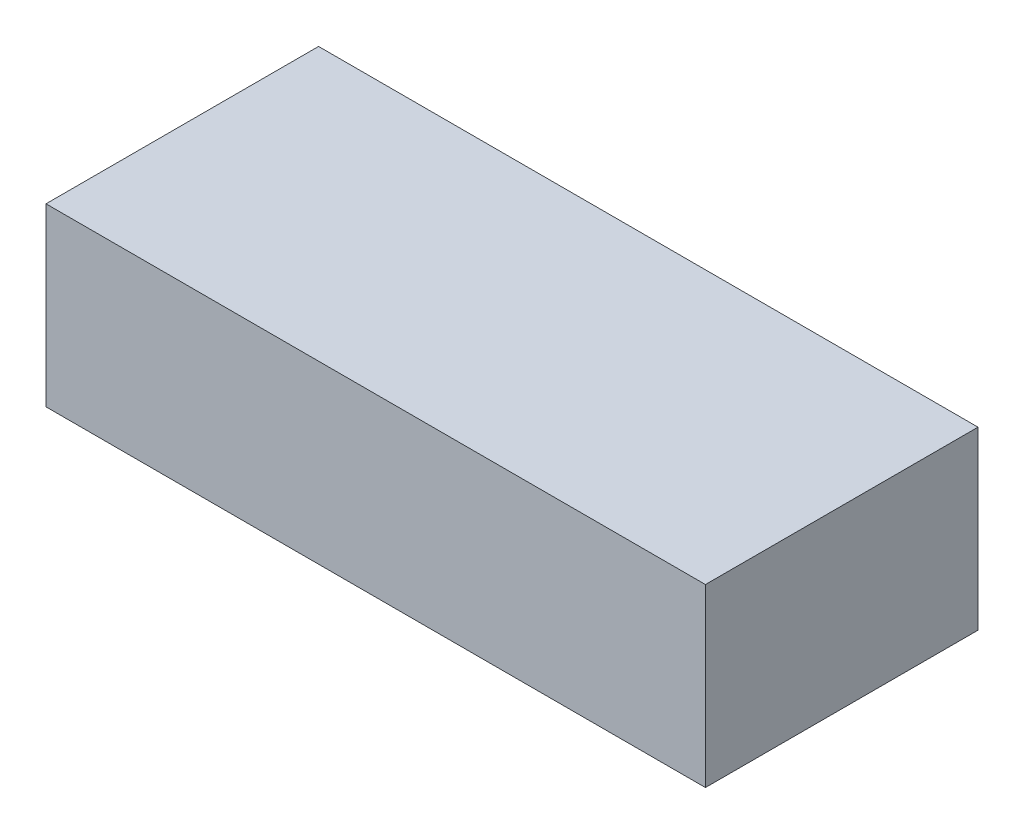
SolidWorks part; units mm, degrees
ref_plane "Front Plane" through (0, 0, 0) normal (0, 0, 1) x (1, 0, 0)
ref_plane "Top Plane" through (0, 0, 0) normal (0, 1, 0) x (1, 0, 0)
ref_plane "Right Plane" through (0, 0, 0) normal (1, 0, 0) x (0, 0, -1)
sketch "Croquis1" plane through (0, 0, 0) normal (0, 1, 0) x (1, 0, 0)
  line L1 (37.5, -15.5) -> (-37.5, -15.5)
  line L2 (37.5, -15.5) -> (37.5, 15.5)
  line L3 (37.5, 15.5) -> (-37.5, 15.5)
  line L4 (-37.5, -15.5) -> (-37.5, 15.5)
  line L5 (37.5, -15.5) -> (-37.5, 15.5) construction
  line L6 (37.5, 15.5) -> (-37.5, -15.5) construction
  point P0 (0, 0)
  dimension "D1" = 75
  dimension "D2" = 31
extrude "Saliente-Extruir1" add sketch "Croquis1" along normal blind 20
